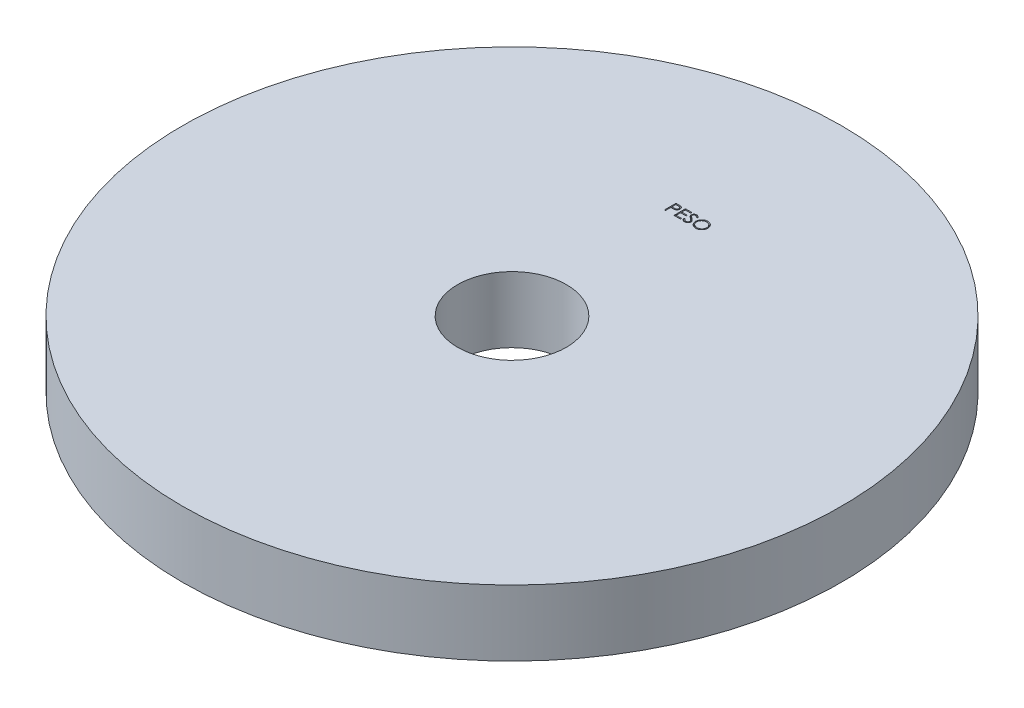
SolidWorks part; units mm, degrees
ref_plane "Plano frontal" through (0, 0, 0) normal (0, 0, 1) x (1, 0, 0)
ref_plane "Plano superior" through (0, 0, 0) normal (0, 1, 0) x (1, 0, 0)
ref_plane "Plano direito" through (0, 0, 0) normal (1, 0, 0) x (0, 0, -1)
sketch "Esboço1" plane through (0, 0, 0) normal (0, 1, 0) x (1, 0, 0)
  circle A0 centre (0, 0) radius 100
  circle A1 centre (0, 0) radius 16.5
  dimension "D1" = 33
  dimension "D2" = 200
extrude "Ressalto-extrusão1" add sketch "Esboço1" along normal blind 20
sketch "Esboço2" plane through (0, 20, 0) normal (0, 1, 0) x (1, 0, 0)
  text T0 "PESO"
extrude "Corte-extrusão1" cut sketch "Esboço2" against normal blind 1
